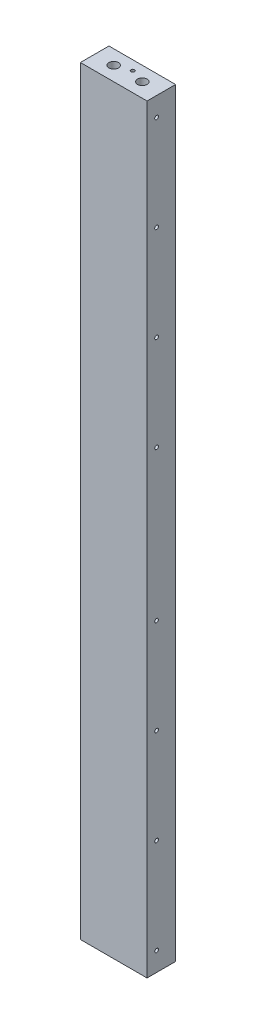
SolidWorks part; units mm, degrees
ref_plane "Front Plane" through (0, 0, 0) normal (0, 0, 1) x (1, 0, 0)
ref_plane "Top Plane" through (0, 0, 0) normal (0, 1, 0) x (1, 0, 0)
ref_plane "Right Plane" through (0, 0, 0) normal (1, 0, 0) x (0, 0, -1)
sketch "Sketch1" plane through (0, 0, 0) normal (0, 1, 0) x (1, 0, 0)
  line L1 (0, 0) -> (88.9, 0)
  line L2 (0, 0) -> (0, -38.1)
  line L3 (0, -38.1) -> (88.9, -38.1)
  line L4 (88.9, 0) -> (88.9, -38.1)
  dimension "D1" = 38.1
  dimension "D2" = 88.9
extrude "Boss-Extrude1" add sketch "Sketch1" along normal blind 1012.825
sketch "Sketch2" plane through (0, 1012.825, 0) normal (0, 1, 0) x (1, 0, 0)
  line L0 (25.4, -19.05) -> (63.5, -19.05) construction
  line L1 (0, 0) -> (0, -38.1) construction
  line L2 (88.9, 0) -> (0, 0) construction
  circle A0 centre (25.4, -19.05) radius 6.35
  circle A1 centre (63.5, -19.05) radius 6.35
  point P7 (0, -19.05)
  point P10 (44.45, 0)
  point P11 (44.45, -19.05)
  dimension "D1" = 12.7
  dimension "D2" = 12.7
  dimension "D3" = 38.1
extrude "Cut-Extrude1" cut sketch "Sketch2" against normal blind 19.05
sketch "Sketch3" plane through (0, 0, 0) normal (0, -1, 0) x (1, 0, 0)
  line L0 (25.4, 19.05) -> (63.5, 19.05) construction
  line L3 (0, 0) -> (0, 38.1) construction
  line L4 (0, 38.1) -> (88.9, 38.1) construction
  circle A0 centre (25.4, 19.05) radius 6.35
  circle A1 centre (63.5, 19.05) radius 6.35
  point P8 (0, 19.05)
  point P11 (44.45, 19.05)
  point P12 (44.45, 38.1)
  dimension "D1" = 12.7
  dimension "D2" = 12.7
  dimension "D3" = 38.1
extrude "Cut-Extrude2" cut sketch "Sketch3" against normal blind 19.05
sketch "Sketch4" plane through (0, 0, 0) normal (0, -1, 0) x (1, 0, 0)
  line L1 (0, 38.1) -> (88.9, 38.1) construction
  line L2 (88.9, 38.1) -> (88.9, 0) construction
  point P0 (76.2, 12.7)
  point P1 (12.7, 19.05)
  dimension "D1" = 12.7
  dimension "D2" = 25.4
  dimension "D3" = 19.05
  dimension "D4" = 76.2
sketch "Sketch5" plane through (0, 1012.825, 0) normal (0, 1, 0) x (1, 0, 0)
  line L0 (88.9, -38.1) -> (88.9, 0) construction
  line L2 (0, -38.1) -> (88.9, -38.1) construction
  point P0 (44.45, -12.7)
  dimension "D1" = 44.45
  dimension "D2" = 25.4
hole_wizard "#10 (0.1935) Diameter Hole1" positions "3DSketch1" profile "Sketch7" hole size "#10" standard "ANSI Inch"
sketch3d "3DSketch1"
  point P0 (44.45, 1012.825, 12.7)
  point P3 (12.7, 0, 19.05)
  point P6 (76.2, 0, 12.7)
sketch "Sketch7" plane through (44.45, 1012.825, 12.7) normal (1, 0, 0) x (0, 0, 1)
  line L0 (0, 0) -> (0, 77.6766)
  line L1 (0, 77.6766) -> (2.4574, 76.2)
  line L2 (2.4574, 76.2) -> (2.4574, 0)
  line L5 (2.4574, 0) -> (0, 0)
  line L10 (0, 77.6766) -> (-2.4575, 76.2) construction
  line L11 (0, -6.35) -> (0, 107.95) construction
  dimension "Hole Dia." = 4.9149
  dimension "Hole Depth" = 76.2
  dimension "Drill Angle" = 118
sketch "Sketch8" plane through (88.9, 0, 0) normal (1, 0, 0) x (0, 0, -1)
  line L0 (-25.4, 0) -> (-25.4, 1012.825) construction
  line L1 (-38.1, 0) -> (0, 0) construction
  line L2 (-38.1, 1012.825) -> (0, 1012.825) construction
  line L3 (-38.1, 1012.825) -> (-38.1, 0) construction
  line L4 (0, 506.4125) -> (-38.1, 506.4125) construction
  line L5 (0, 1012.825) -> (0, 0) construction
  point P8 (-25.4, 25.4)
  point P9 (-25.4, 152.4)
  point P10 (-25.4, 406.4)
  point P11 (-25.4, 279.4)
  point P12 (-25.4, 987.425)
  point P13 (-25.4, 860.425)
  point P18 (-25.4, 733.425)
  point P19 (-25.4, 606.425)
  dimension "D1" = 12.7
  dimension "D2" = 25.4
  dimension "D3" = 127
  dimension "D4" = 127
  dimension "D5" = 127
hole_wizard "#10 (0.1935) Diameter Hole2" positions "3DSketch2" profile "Sketch10" hole size "#10" standard "ANSI Inch"
sketch3d "3DSketch2"
  point P0 (88.9, 987.425, 25.4)
  point P3 (88.9, 860.425, 25.4)
  point P6 (88.9, 733.425, 25.4)
  point P9 (88.9, 606.425, 25.4)
  point P12 (88.9, 406.4, 25.4)
  point P15 (88.9, 279.4, 25.4)
  point P18 (88.9, 152.4, 25.4)
  point P21 (88.9, 25.4, 25.4)
sketch "Sketch10" plane through (88.9, 987.425, 25.4) normal (0, 1, 0) x (0, 0, -1)
  line L0 (0, 0) -> (0, 52.2766)
  line L1 (0, 52.2766) -> (2.4574, 50.8)
  line L2 (2.4574, 50.8) -> (2.4574, 0)
  line L5 (2.4574, 0) -> (0, 0)
  line L10 (0, 52.2766) -> (-2.4575, 50.8) construction
  line L11 (0, -6.35) -> (0, 107.95) construction
  dimension "Hole Dia." = 4.9149
  dimension "Hole Depth" = 50.8
  dimension "Drill Angle" = 118
